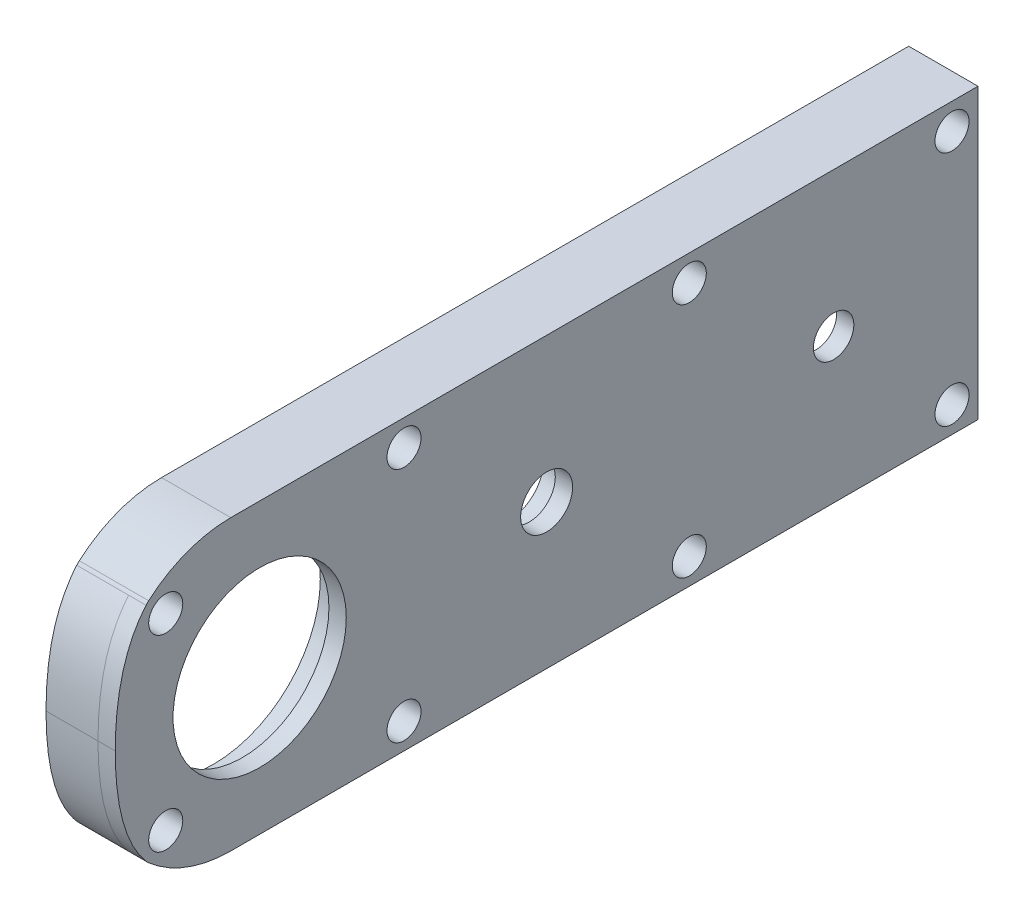
SolidWorks part; units mm, degrees
ref_plane "Front Plane" through (0, 0, 0) normal (0, 0, 1) x (1, 0, 0)
ref_plane "Top Plane" through (0, 0, 0) normal (0, 1, 0) x (1, 0, 0)
ref_plane "Right Plane" through (0, 0, 0) normal (1, 0, 0) x (0, 0, -1)
sketch "Sketch1" plane through (0, 0, 0) normal (1, 0, 0) x (0, 0, -1)
  circle A0 centre (0, 0) radius 18.5
  circle A1 centre (0, 0) radius 23
  circle A2 centre (49.7, 0) radius 6 construction
  circle A3 centre (49.7, 0) radius 9.5 construction
  circle A4 centre (99.4, 0) radius 3.5 construction
  dimension "D1" = 37
  dimension "D3" = 12
  dimension "D6" = 7
  dimension "D4" = 49.7
  dimension "D7" = 49.7
  dimension "D2" = 4.5
  dimension "D5" = 3.5
extrude "Boss-Extrude1" add sketch "Sketch1" against normal blind 5
sketch "Sketch2" plane through (0, 0, 0) normal (1, 0, 0) x (0, 0, -1)
  circle A0 centre (49.7, 0) radius 9.5 construction
  circle A1 centre (49.7, 0) radius 6 construction
  circle A2 centre (49.7, 0) radius 9.5
  circle A3 centre (49.7, 0) radius 6
extrude "Boss-Extrude2" add sketch "Sketch2" against normal blind 3.5 separate body
sketch "Sketch3" plane through (0, 0, 0) normal (1, 0, 0) x (0, 0, -1)
  line L1 (-25, -25) -> (124.4, -25)
  line L2 (-25, -25) -> (-25, 25)
  line L3 (-25, 25) -> (124.4, 25)
  line L4 (124.4, -25) -> (124.4, 25)
  line L5 (-25, -25) -> (124.4, 25) construction
  line L6 (-25, 25) -> (124.4, -25) construction
  circle A0 centre (49.7, 0) radius 6 construction
  circle A1 centre (49.7, 0) radius 6 construction
  circle A2 centre (0, 0) radius 15
  circle A3 centre (49.7, 0) radius 4.5
  circle A4 centre (99.4, 0) radius 3.5 construction
  circle A5 centre (99.4, 0) radius 3.5
  point P0 (49.7, 0)
  dimension "D4" = 30
  dimension "D5" = 9
  dimension "D1" = 25
  dimension "D2" = 25
  dimension "D3" = 149.4
extrude "Boss-Extrude3" add sketch "Sketch3" along normal blind 3
sketch "Sketch4" plane through (0, 0, 0) normal (-1, 0, 0) x (0, 0, 1)
  line L0 (25, 25) -> (25, -25) construction
  line L1 (-124.4, 25) -> (25, 25) construction
  line L2 (-124.4, -25) -> (-124.4, 25) construction
  line L3 (0, 0) -> (25, 0) construction
  line L5 (5, 22.5) -> (16.4689, 22.5) construction
  line L6 (16.4689, 22.5) -> (5, 22.5) construction
  line L7 (-4.7697, 22.5) -> (-20.9689, 22.5)
  line L11 (-29.0311, 22.5) -> (-70.3689, 22.5)
  line L12 (-124.4, 0) -> (-121.9, 0)
  line L13 (-121.9, 0) -> (-121.9, 16.4689)
  line L14 (-78.4311, 22.5) -> (-115.8689, 22.5)
  line L15 (-124.4, 0) -> (-124.4, 25)
  line L16 (-124.4, 25) -> (-25, 25)
  line L17 (16.2635, 16.2635) -> (0, 0) construction
  line L18 (-25, 25) -> (5, 25)
  line L19 (18.5, 0) -> (25, 0)
  line L20 (25, 0) -> (25, 13) construction
  line L21 (25, 13) -> (19.6767, 19.196) construction
  circle A0 centre (20.5, 20.5) radius 4.5 construction
  arc A1 (-29.0311, 22.5) -> (-20.9689, 22.5) centre (-25, 20.5) ccw
  arc A2 (-121.9, 16.4689) -> (-115.8689, 22.5) centre (-119.9, 20.5) ccw
  arc A3 (-78.4311, 22.5) -> (-70.3689, 22.5) centre (-74.4, 20.5) ccw
  circle A4 centre (-99.4, 0) radius 3.5 construction
  arc A5 (19.6767, 19.196) -> (19.2291, 19.648) centre (16.2635, 16.2635) ccw
  circle A6 centre (0, 0) radius 23 construction
  circle A9 centre (0, 0) radius 18.5 construction
  arc A10 (5, 25) -> (19.2291, 19.648) centre (5, 3.409) cw
  arc A11 (18.5, 0) -> (13.0815, 13.0815) centre (0, 0) ccw
  arc A13 (12.7855, 19.1189) -> (13.0815, 13.0815) centre (16.2635, 16.2635) ccw
  arc A15 (12.7855, 19.1189) -> (-4.7697, 22.5) centre (0, 0) ccw
  spline S0 degree 2 poles (25, 0) (25, 13) (19.6767, 19.196) knots 0 0 0 1 1 1
  dimension "D1" = 9
  dimension "D2" = 45.5
  dimension "D3" = 25
  dimension "D4" = 45
  dimension "D5" = 2.5
  dimension "D6" = 2.5
  dimension "D7" = 5
  dimension "D8" = 13
extrude "Boss-Extrude4" add sketch "Sketch4" along normal blind 9
sketch "Sketch5" plane through (0, 0, 0) normal (-1, 0, 0) x (0, 0, 1)
  line L2 (25, 0) -> (25, 25)
  line L3 (25, 25) -> (5, 25)
  line L4 (25, 0) -> (25, 25)
  line L5 (25, 25) -> (5, 25)
  arc A2 (19.6767, 19.196) -> (19.2291, 19.648) centre (16.2635, 16.2635) ccw
  arc A3 (19.2291, 19.648) -> (5, 25) centre (5, 3.409) ccw
  arc A4 (19.6767, 19.196) -> (19.2291, 19.648) centre (16.2635, 16.2635) ccw
  arc A5 (19.2291, 19.648) -> (5, 25) centre (5, 3.409) ccw
  parabola Q1 (19.6767, 19.196) -> (25, 0) focus (12.9458, 15.4073) apex (17.5227, 21.2574)
  parabola Q2 (19.6767, 19.196) -> (25, 0) focus (12.9458, 15.4073) apex (17.5227, 21.2574)
  dimension "D1" = 0
extrude "Cut-Extrude1" cut sketch "Sketch5" against normal through all both and the other way through all
sketch "Sketch6" plane through (-9, 0, 0) normal (-1, 0, 0) x (0, 0, 1)
  circle A0 centre (16.2635, 16.2635) radius 2
  circle A1 centre (-25, 20.5) radius 2
  circle A2 centre (-74.4, 20.5) radius 2
  circle A3 centre (-119.9, 20.5) radius 2
  dimension "D1" = 4
extrude "Cut-Extrude2" cut sketch "Sketch6" against normal through all
sketch "Sketch7" plane through (3, 0, 0) normal (1, 0, 0) x (0, 0, -1)
  circle A0 centre (-16.2635, 16.2635) radius 2.95
  circle A1 centre (25, 20.5) radius 2.95
  circle A2 centre (74.4, 20.5) radius 2.95
  circle A3 centre (119.9, 20.5) radius 2.95
  dimension "D1" = 5.9
extrude "Cut-Extrude3" cut sketch "Sketch7" against normal blind 5
mirror "Mirror1" about plane through (0, 0, 0) normal (0, 1, 0) of "Cut-Extrude3", "Cut-Extrude2", "Cut-Extrude1", "Boss-Extrude4"
